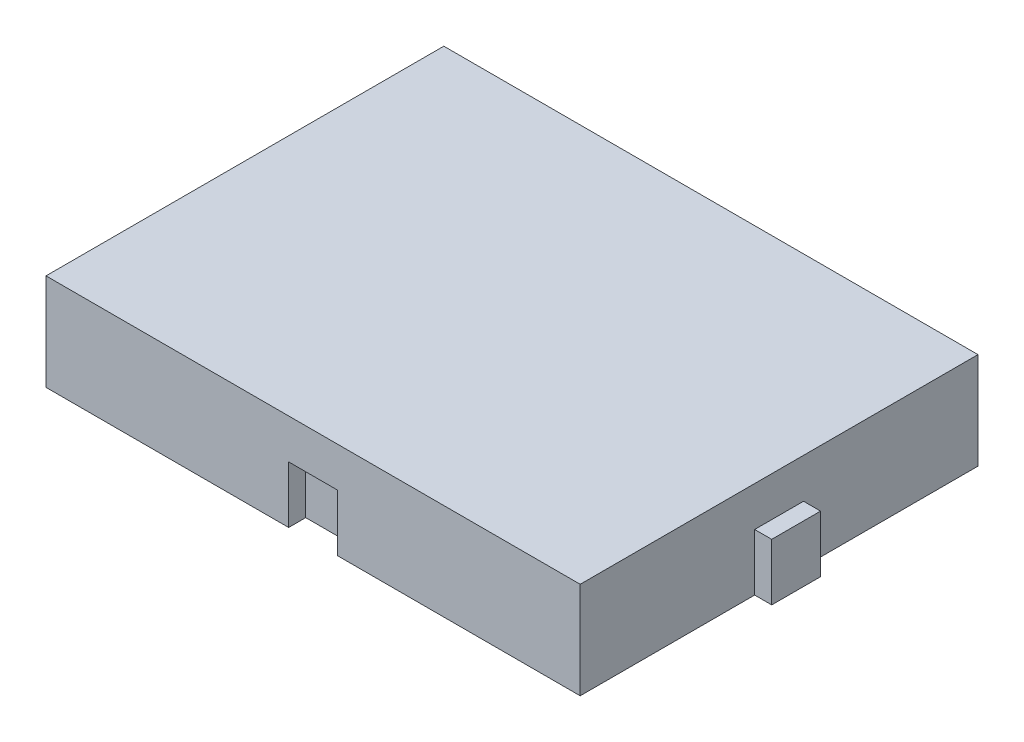
SolidWorks part; units mm, degrees
ref_plane "Front Plane" through (0, 0, 0) normal (0, 0, 1) x (1, 0, 0)
ref_plane "Top Plane" through (0, 0, 0) normal (0, 1, 0) x (1, 0, 0)
ref_plane "Right Plane" through (0, 0, 0) normal (1, 0, 0) x (0, 0, -1)
sketch "Sketch1" plane through (0, 0, 0) normal (0, 1, 0) x (1, 0, 0)
  line L1 (-23.5, -17.5) -> (23.5, -17.5)
  line L2 (-23.5, -17.5) -> (-23.5, 17.5)
  line L3 (-23.5, 17.5) -> (23.5, 17.5)
  line L4 (23.5, -17.5) -> (23.5, 17.5)
  line L5 (-23.5, -17.5) -> (23.5, 17.5) construction
  line L6 (-23.5, 17.5) -> (23.5, -17.5) construction
  point P0 (0, 0)
  dimension "D1" = 47
  dimension "D2" = 35
extrude "Boss-Extrude1" add sketch "Sketch1" along normal blind 8.5
sketch "Sketch2" plane through (0, 0, 0) normal (0, -1, 0) x (-1, 0, 0)
  line L0 (23.5, -17.5) -> (-23.5, -17.5) construction
  line L1 (2.15, 19) -> (-2.15, 19)
  line L2 (2.15, 19) -> (2.15, 17.5)
  line L3 (2.15, 17.5) -> (-2.15, 17.5)
  line L4 (-2.15, 19) -> (-2.15, 17.5)
  line L5 (-23.5, -17.5) -> (-23.5, 17.5) construction
  line L6 (-23.5, -2.15) -> (-25, -2.15)
  line L7 (-23.5, -2.15) -> (-23.5, 2.15)
  line L8 (-23.5, 2.15) -> (-25, 2.15)
  line L9 (-25, -2.15) -> (-25, 2.15)
  line L11 (-23.5, 17.5) -> (23.5, 17.5) construction
  point P12 (0, -17.5)
  point P13 (0, 17.5)
  point P14 (-25, 0)
  dimension "D1" = 4.3
  dimension "D2" = 1.5
extrude "Boss-Extrude2" add sketch "Sketch2" against normal blind 5
sketch "Sketch3" plane through (0, 0, 0) normal (0, -1, 0) x (-1, 0, 0)
  line L1 (-2.15, -16) -> (2.15, -16)
  line L2 (-2.15, -16) -> (-2.15, -17.5)
  line L3 (-2.15, -17.5) -> (2.15, -17.5)
  line L4 (2.15, -16) -> (2.15, -17.5)
  line L5 (23.5, 17.5) -> (23.5, -17.5) construction
  line L6 (23.5, -2.15) -> (22, -2.15)
  line L7 (23.5, -2.15) -> (23.5, 2.15)
  line L8 (23.5, 2.15) -> (22, 2.15)
  line L9 (22, -2.15) -> (22, 2.15)
  line L10 (23.5, -17.5) -> (-23.5, -17.5) construction
  point P12 (23.5, 0)
  point P13 (23.5, 0)
  point P14 (0, -17.5)
  dimension "D1" = 4.3
  dimension "D2" = 1.5
extrude "Cut-Extrude1" cut sketch "Sketch3" against normal blind 5
